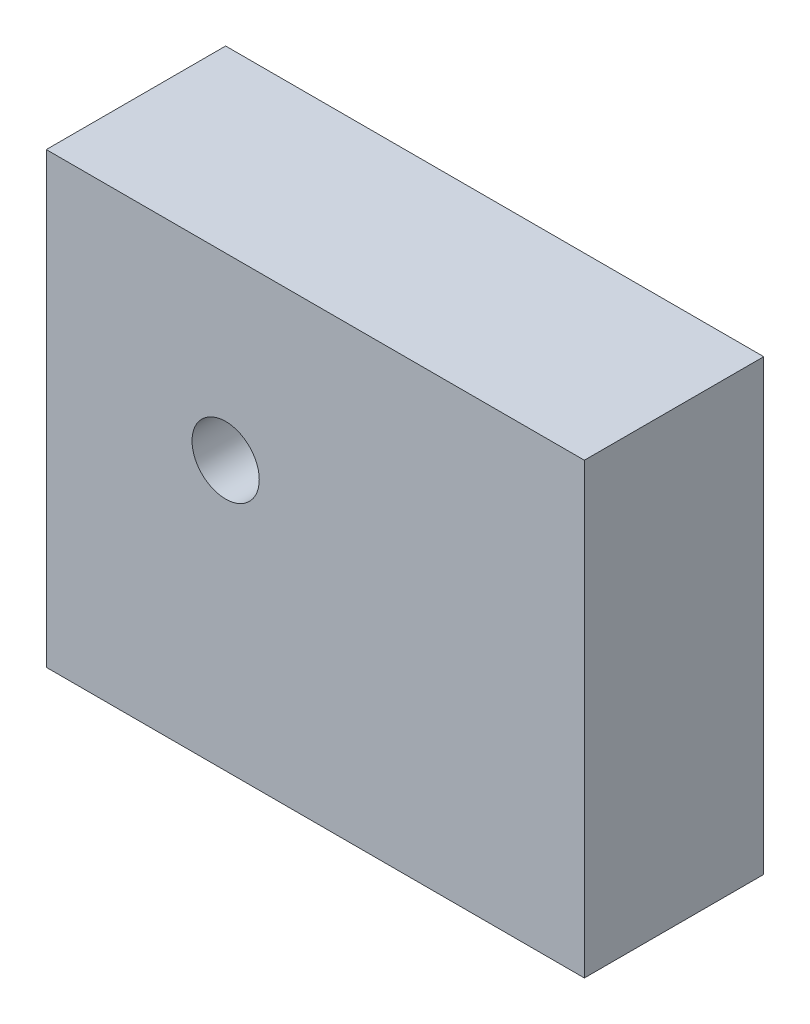
SolidWorks part; units mm, degrees
ref_plane "Front Plane" through (0, 0, 0) normal (0, 0, 1) x (1, 0, 0)
ref_plane "Top Plane" through (0, 0, 0) normal (0, 1, 0) x (1, 0, 0)
ref_plane "Right Plane" through (0, 0, 0) normal (1, 0, 0) x (0, 0, -1)
sketch "Sketch1" plane through (0, 0, 0) normal (0, 0, 1) x (1, 0, 0)
  line L1 (0, 0) -> (76.2, 0)
  line L2 (0, 0) -> (0, 63.5)
  line L3 (0, 63.5) -> (76.2, 63.5)
  line L4 (76.2, 0) -> (76.2, 63.5)
  circle A0 centre (25.4, 38.1) radius 4.7625
  point P7 (0, 0)
  point P9 (26.344, 9.1524)
  dimension "D3" = 9.525
  dimension "D1" = 76.2
  dimension "D2" = 63.5
  dimension "D4" = 50.8
  dimension "D5" = 38.1
extrude "Boss-Extrude1" add sketch "Sketch1" along normal blind 25.4
